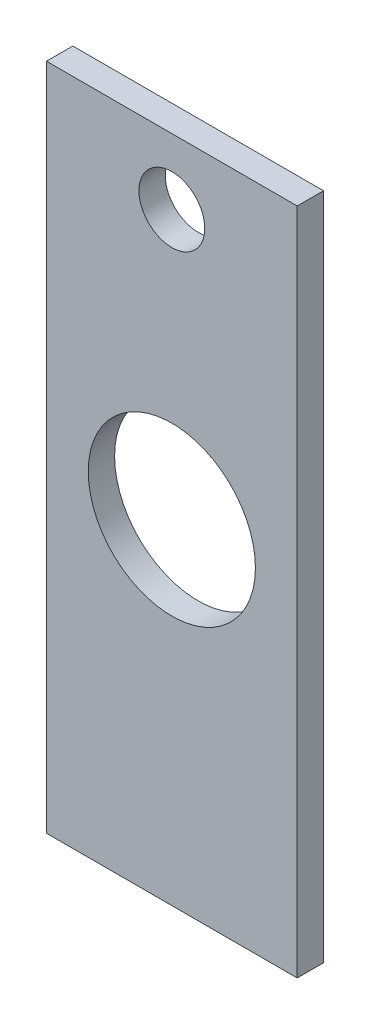
SolidWorks part; units mm, degrees
ref_plane "Front Plane" through (0, 0, 0) normal (0, 0, 1) x (1, 0, 0)
ref_plane "Top Plane" through (0, 0, 0) normal (0, 1, 0) x (1, 0, 0)
ref_plane "Right Plane" through (0, 0, 0) normal (1, 0, 0) x (0, 0, -1)
sketch "Sketch1" plane through (0, 0, 0) normal (0, 0, 1) x (1, 0, 0)
  line L0 (0, 0) -> (34.0689, 0) construction
  line L1 (-9.525, 25.4) -> (9.525, 25.4)
  line L2 (-9.525, 25.4) -> (-9.525, -25.4)
  line L3 (-9.525, -25.4) -> (9.525, -25.4)
  line L4 (9.525, 25.4) -> (9.525, -25.4)
  line L5 (0, 0) -> (0, 12.9445) construction
  circle A0 centre (0, 0) radius 6.35
  dimension "D3" = 12.7
  dimension "D1" = 50.8
  dimension "D2" = 19.05
extrude "Boss-Extrude1" add sketch "Sketch1" along normal blind 2
hole_wizard "Ø5.0 (5) Diameter Hole1" positions "Sketch4" profile "Sketch3" hole size "Ø5.0" standard "ANSI Metric"
sketch "Sketch4" plane through (0, 0, 0) normal (0, 0, -1) x (-1, 0, 0)
  line L0 (-9.525, 25.4) -> (9.525, 25.4) construction
  line L2 (9.525, 25.4) -> (9.525, -25.4) construction
  point P0 (0, 20.4)
  dimension "D1" = 5
  dimension "D2" = 9.525
sketch "Sketch3" plane through (0, 20.4, 0) normal (1, 0, 0) x (0, 1, 0)
  line L0 (0, 0) -> (0, 6.5022)
  line L1 (0, 6.5022) -> (2.5, 5)
  line L2 (2.5, 5) -> (2.5, 0)
  line L5 (2.5, 0) -> (0, 0)
  line L10 (0, 6.5022) -> (-2.5, 5) construction
  line L11 (0, -6.35) -> (0, 107.95) construction
  dimension "Hole Dia." = 5
  dimension "Hole Depth" = 5
  dimension "Drill Angle" = 118
